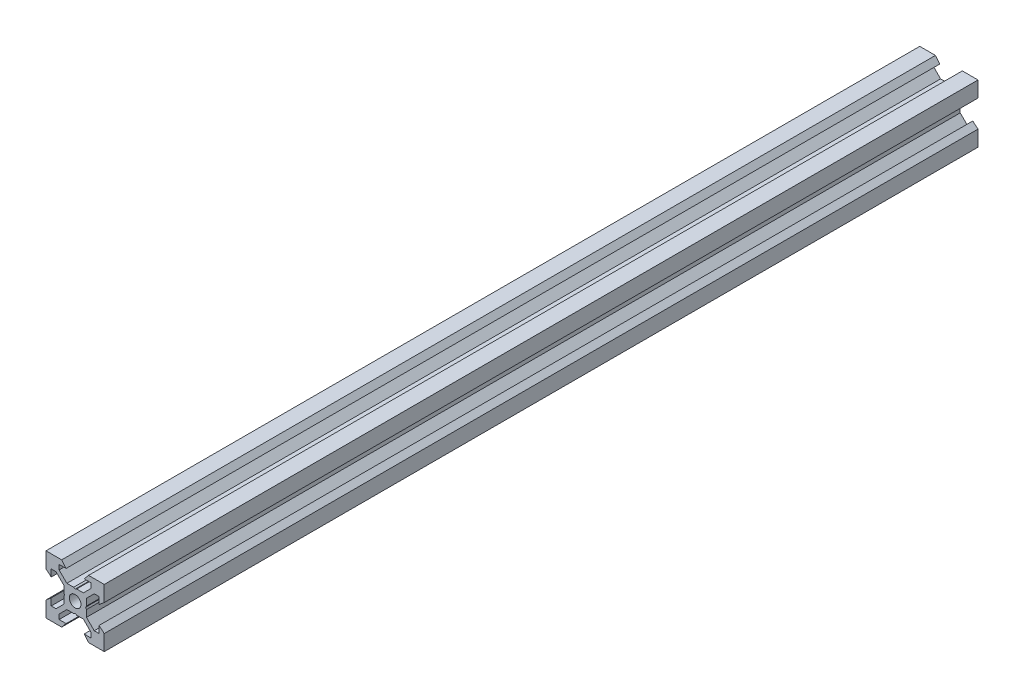
SolidWorks part; units mm, degrees
ref_plane "Front Plane" through (0, 0, 0) normal (0, 0, 1) x (1, 0, 0)
ref_plane "Top Plane" through (0, 0, 0) normal (0, 1, 0) x (1, 0, 0)
ref_plane "Right Plane" through (0, 0, 0) normal (1, 0, 0) x (0, 0, -1)
sketch "Sketch1" plane through (0, 0, 0) normal (0, 0, 1) x (1, 0, 0)
  line L0 (10, 10) -> (4.6104, 10) construction
  line L1 (10, 10) -> (10, 4.6104) construction
  line L2 (10, -10) -> (10, -4.6104) construction
  line L3 (10, -10) -> (4.6104, -10) construction
  line L4 (10, 10) -> (10, 4.6104)
  line L5 (6.5607, 5.5) -> (8.2, 5.5)
  line L6 (5.5, 8.2) -> (5.5, 6.5607)
  line L7 (10, 10) -> (4.6104, 10)
  line L8 (10, 10) -> (10, 4.6104)
  line L9 (6.5607, 5.5) -> (3.9, 2.8393)
  line L10 (5.5, 6.5607) -> (2.8393, 3.9)
  line L11 (10, 4.6104) -> (8.2, 3.1)
  line L12 (4.6104, 10) -> (3.1, 8.2)
  line L13 (8.2, 3.1) -> (8.2, 5.5)
  line L14 (3.1, 8.2) -> (5.5, 8.2)
  line L15 (-6.5607, 5.5) -> (-8.2, 5.5)
  line L16 (6.5607, -5.5) -> (8.2, -5.5)
  line L17 (3.1, -8.2) -> (5.5, -8.2)
  line L18 (8.2, -3.1) -> (8.2, -5.5)
  line L19 (4.6104, -10) -> (3.1, -8.2)
  line L20 (10, -4.6104) -> (8.2, -3.1)
  line L21 (0.5196, -3.9) -> (0, -3.6)
  line L22 (0.5196, 3.9) -> (0, 3.6)
  line L23 (3.6, 0) -> (3.9, -0.5196)
  line L24 (3.9, 0.5196) -> (3.6, 0)
  line L25 (3.9, 0.5196) -> (3.9, 2.8393)
  line L26 (2.8393, 3.9) -> (0.5196, 3.9)
  line L27 (3.9, -2.8393) -> (3.9, -0.5196)
  line L28 (2.8393, -3.9) -> (0.5196, -3.9)
  line L29 (5.5, -6.5607) -> (2.8393, -3.9)
  line L30 (6.5607, -5.5) -> (3.9, -2.8393)
  line L31 (10, -10) -> (10, -4.6104)
  line L32 (10, -10) -> (4.6104, -10)
  line L33 (5.5, -8.2) -> (5.5, -6.5607)
  line L34 (-6.5607, -5.5) -> (-8.2, -5.5)
  line L35 (10, -10) -> (10, -4.6104)
  line L36 (0, 0) -> (0, 8.2) construction
  line L37 (-10, -10) -> (-4.6104, -10) construction
  line L38 (-10, -10) -> (-10, -4.6104) construction
  line L39 (-10, 10) -> (-10, 4.6104) construction
  line L40 (-10, 10) -> (-4.6104, 10) construction
  line L41 (-10, -10) -> (-10, -4.6104)
  line L43 (-5.5, -8.2) -> (-5.5, -6.5607)
  line L44 (-10, -10) -> (-4.6104, -10)
  line L45 (-10, -10) -> (-10, -4.6104)
  line L46 (-6.5607, -5.5) -> (-3.9, -2.8393)
  line L47 (-5.5, -6.5607) -> (-2.8393, -3.9)
  line L48 (-2.8393, -3.9) -> (-0.5196, -3.9)
  line L49 (-3.9, -2.8393) -> (-3.9, -0.5196)
  line L50 (-2.8393, 3.9) -> (-0.5196, 3.9)
  line L51 (-3.9, 0.5196) -> (-3.9, 2.8393)
  line L52 (-3.9, 0.5196) -> (-3.6, 0)
  line L53 (-3.6, 0) -> (-3.9, -0.5196)
  line L54 (-0.5196, 3.9) -> (0, 3.6)
  line L55 (-0.5196, -3.9) -> (0, -3.6)
  line L56 (-10, -4.6104) -> (-8.2, -3.1)
  line L57 (-4.6104, -10) -> (-3.1, -8.2)
  line L58 (-8.2, -3.1) -> (-8.2, -5.5)
  line L59 (-3.1, -8.2) -> (-5.5, -8.2)
  line L60 (-10, -10) -> (10, -10) construction
  line L61 (-10, -10) -> (-10, 10) construction
  line L62 (-3.1, 8.2) -> (-5.5, 8.2)
  line L63 (-8.2, 3.1) -> (-8.2, 5.5)
  line L64 (-4.6104, 10) -> (-3.1, 8.2)
  line L65 (-10, 4.6104) -> (-8.2, 3.1)
  line L66 (-5.5, 6.5607) -> (-2.8393, 3.9)
  line L67 (-6.5607, 5.5) -> (-3.9, 2.8393)
  line L68 (-10, 10) -> (-10, 4.6104)
  line L69 (-10, 10) -> (-4.6104, 10)
  line L70 (-5.5, 8.2) -> (-5.5, 6.5607)
  line L71 (-10, 10) -> (10, 10) construction
  line L72 (-10, 10) -> (-10, 4.6104)
  line L73 (10, -10) -> (10, 10) construction
  line L74 (-10, -10) -> (10, 10) construction
  line L75 (-10, 10) -> (10, -10) construction
  circle A0 centre (0, 0) radius 2
  dimension "D7" = 4
  dimension "D1" = 20
  dimension "D2" = 5.3896
  dimension "D3" = 4.5
  dimension "D4" = 50
  dimension "D5" = 1.8
  dimension "D6" = 1.5104
  dimension "D8" = 5.5
  dimension "D9" = 120
  dimension "D10" = 0.3
  dimension "D11" = 2.3197
  dimension "D12" = 7.8
  dimension "D13" = 7.8
  dimension "D14" = 1.5
  dimension "D15" = 2.6607
extrude "Boss-Extrude1" add sketch "Sketch1" along normal mid plane 300 contours L70 L62 L64 L69 L68 L65 L63 L15 L67 L51 L52 L53 L49 L46 L34 L58 L56 L41 L44 L57 L59 L43 L47 L48 L55 L21 L28 L29 L33 L17 L19 L32 L31 L20 L18 L16 L30 L27 L23 L24 L25 L9 L5 L13 L11 L4 L7 L12 L14 L6 L10
